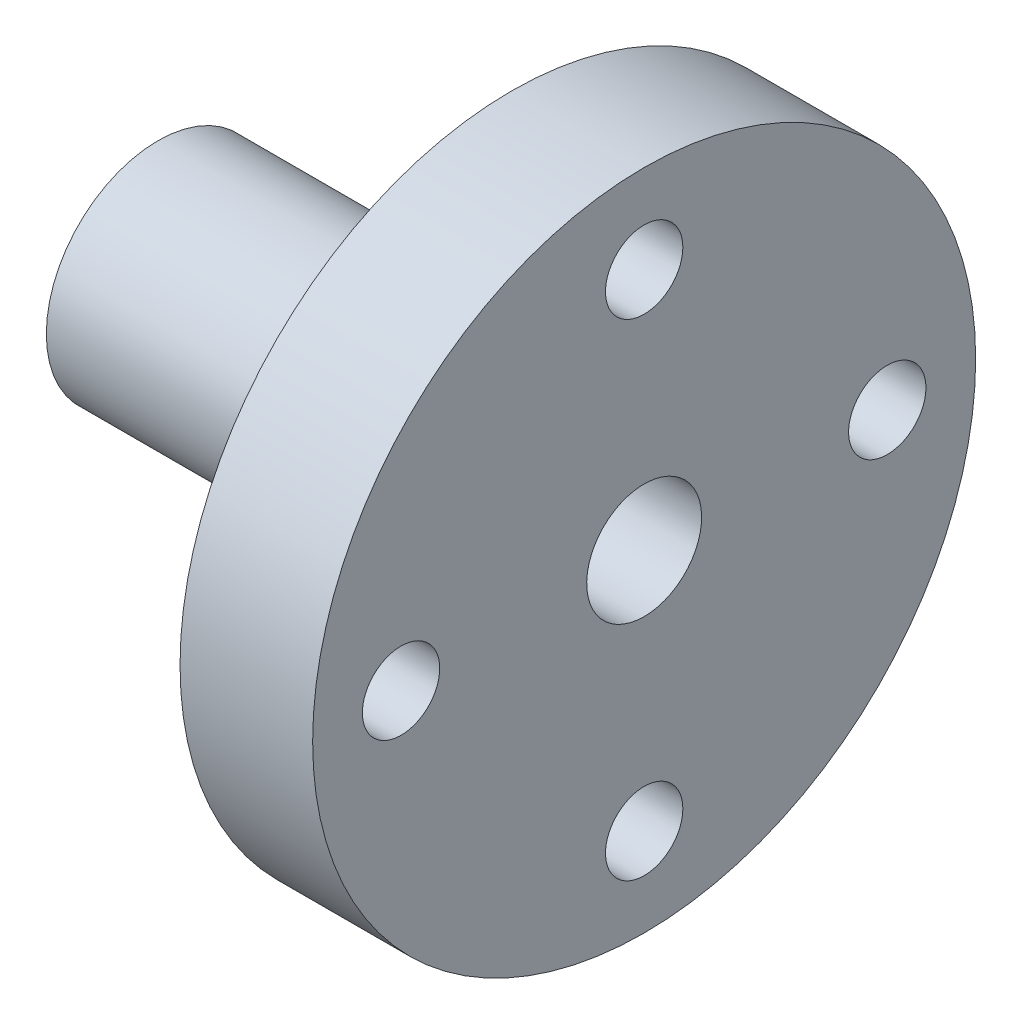
SolidWorks part; units mm, degrees
material "PMMA"
ref_plane "Plan de face" through (0, 0, 0) normal (0, 0, 1) x (1, 0, 0)
ref_plane "Plan de dessus" through (0, 0, 0) normal (0, 1, 0) x (1, 0, 0)
ref_plane "Plan de droite" through (0, 0, 0) normal (1, 0, 0) x (0, 0, -1)
sketch "Esquisse1" plane through (0, 0, 0) normal (0, 0, 1) x (1, 0, 0)
  line L0 (0, 2.25) -> (0, 5.05)
  line L1 (0, 5.05) -> (13, 5.05)
  line L2 (16, 8) -> (16, 15)
  line L3 (16, 15) -> (22, 15)
  line L4 (22, 15) -> (22, 2.6)
  line L5 (22, 2.6) -> (6, 2.6)
  line L6 (6, 2.6) -> (6, 1.2)
  line L7 (6, 1.2) -> (3, 1.2)
  line L8 (3, 1.2) -> (3, 2.25)
  line L9 (3, 2.25) -> (0, 2.25)
  line L10 (0, 0) -> (22, 0) construction
  line L11 (13, 5.05) -> (13, 8)
  line L12 (13, 8) -> (16, 8)
  dimension "D1" = 2.25
  dimension "D2" = 5.05
  dimension "D3" = 15
  dimension "D4" = 16
  dimension "D5" = 22
  dimension "D6" = 1.2
  dimension "D7" = 2.6
  dimension "D8" = 3
  dimension "D9" = 3
  dimension "D10" = 8
  dimension "D11" = 13
revolve "Révolution1" add sketch "Esquisse1" angle 360 about L10
sketch "Esquisse2" plane through (22, 0, 0) normal (1, 0, 0) x (0, 0, -1)
  line L0 (-11, 0) -> (0, 0) construction
  line L1 (0, 0) -> (11, 0) construction
  line L2 (0, 11) -> (0, 0) construction
  line L3 (0, 0) -> (0, -11) construction
  circle A0 centre (0, 11) radius 1.75
  circle A1 centre (11, 0) radius 1.75
  circle A2 centre (0, -11) radius 1.75
  circle A3 centre (-11, 0) radius 1.75
  dimension "D1" = 3.5
  dimension "D2" = 11
extrude "Enlèv. mat.-Extru.1" cut sketch "Esquisse2" against normal up to next
ref_plane "Plan1" through (3, 0, 0) normal (-1, 0, 0) x (0, 0, 1)
sketch "Esquisse3" plane through (3, 0, 0) normal (-1, 0, 0) x (0, 0, 1)
  line L0 (0, 0) -> (2.5461, 0) construction
  line L1 (2.5461, 0) -> (2.1634, -0.3827)
  line L2 (2.5461, 0) -> (2.1644, 0.3817)
  line L3 (2.1644, 0.3817) -> (2.1634, -0.3827)
  dimension "D1" = 45
extrude "Enlèv. mat.-Extru.2" cut sketch "Esquisse3" along normal blind 10
pattern_circular "Répétition circulaire1" count 24 over 360 about axis through (0, 0, 0) along (1, 0, 0) of "Enlèv. mat.-Extru.2"
